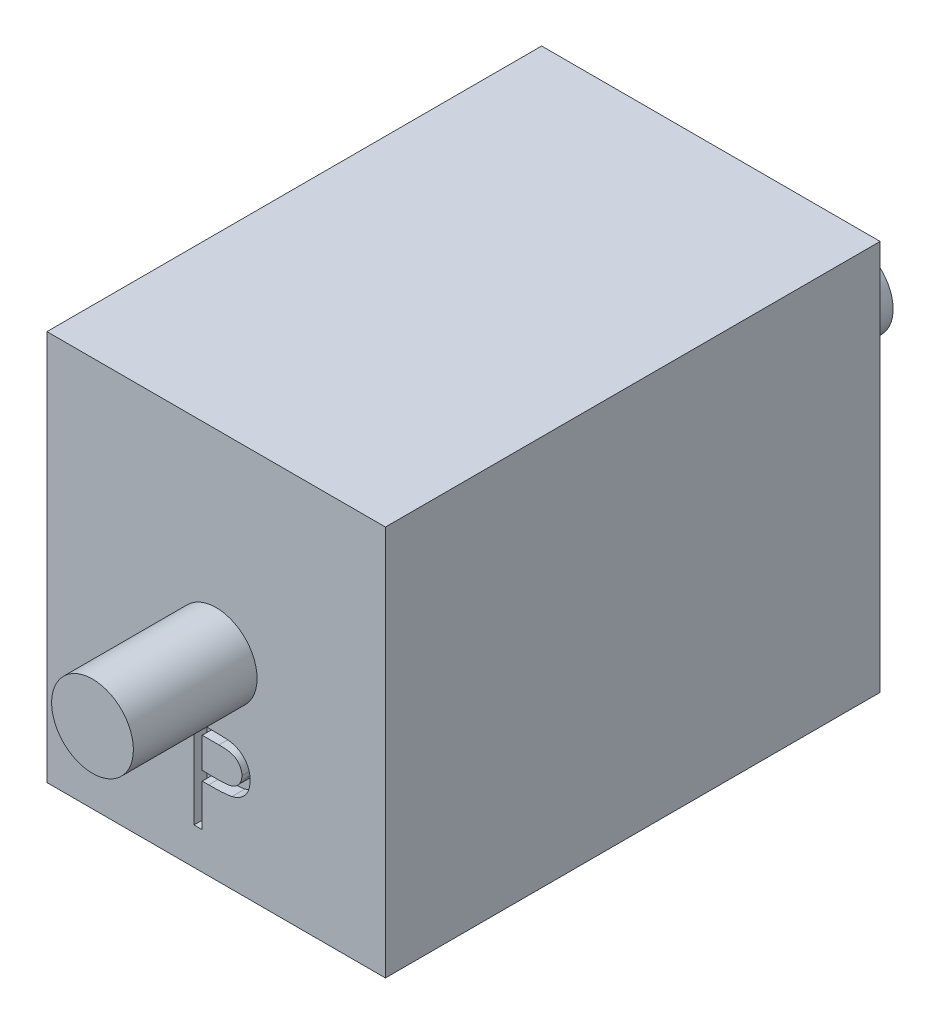
SolidWorks part; units mm, degrees
ref_plane "Front Plane" through (0, 0, 0) normal (0, 0, 1) x (1, 0, 0)
ref_plane "Top Plane" through (0, 0, 0) normal (0, 1, 0) x (1, 0, 0)
ref_plane "Right Plane" through (0, 0, 0) normal (1, 0, 0) x (0, 0, -1)
sketch "Sketch1" plane through (0, 0, 0) normal (0, 0, 1) x (1, 0, 0)
  line L1 (6.5, -7.5) -> (-6.5, -7.5)
  line L2 (6.5, -7.5) -> (6.5, 7.5)
  line L3 (6.5, 7.5) -> (-6.5, 7.5)
  line L4 (-6.5, -7.5) -> (-6.5, 7.5)
  line L5 (6.5, -7.5) -> (-6.5, 7.5) construction
  line L6 (6.5, 7.5) -> (-6.5, -7.5) construction
  point P0 (0, 0)
  dimension "D1" = 15
  dimension "D2" = 13
extrude "Boss-Extrude1" add sketch "Sketch1" along normal blind 19
sketch "Sketch2" plane through (0, 0, 19) normal (0, 0, 1) x (1, 0, 0)
  circle A0 centre (0, 0) radius 1.57
  dimension "D1" = 3.14
extrude "Boss-Extrude2" add sketch "Sketch2" along normal blind 4.75
sketch "Sketch3" plane through (0, 0, 0) normal (0, 0, -1) x (-1, 0, 0)
  circle A0 centre (0, 0) radius 1.5
  dimension "D1" = 3
extrude "Boss-Extrude3" add sketch "Sketch3" along normal blind 5.5
sketch "Sketch4" plane through (0, 0, 0) normal (0, 0, -1) x (-1, 0, 0)
  text T0 "M"
extrude "Cut-Extrude1" cut sketch "Sketch4" against normal blind 0.5
sketch "Sketch5" plane through (0, 0, 19) normal (0, 0, 1) x (1, 0, 0)
  text T0 "P"
extrude "Cut-Extrude2" cut sketch "Sketch5" against normal blind 0.5
